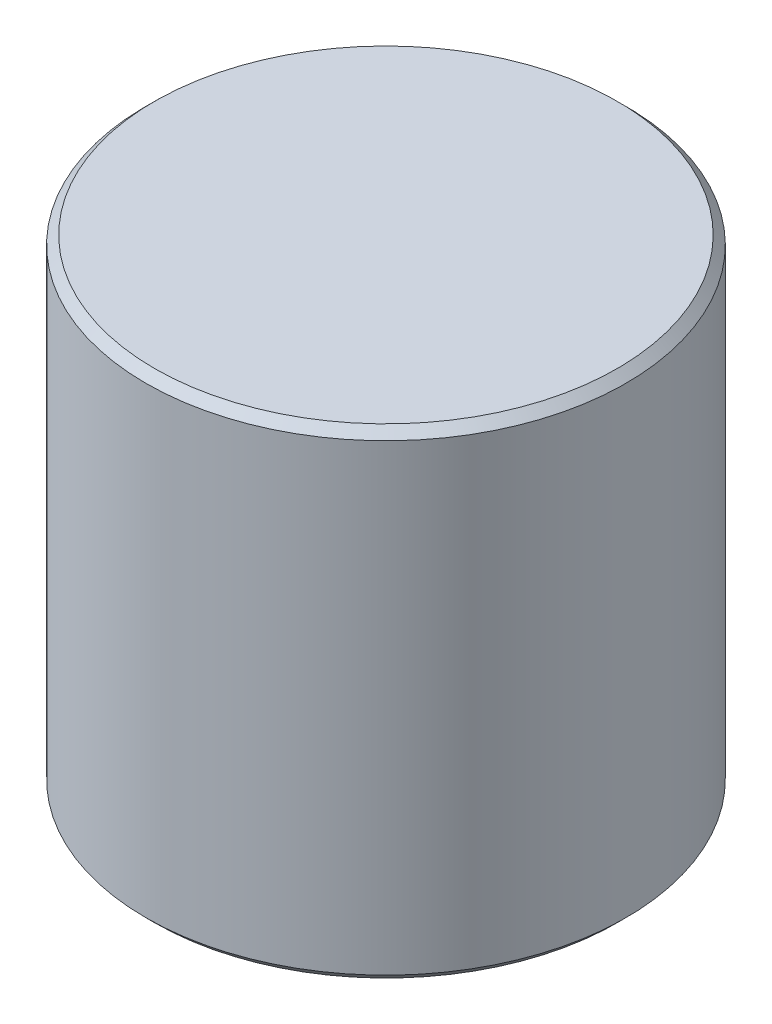
SolidWorks part; units mm, degrees
material "AISI 416 Annealed Stainless Steel (SS)"
ref_plane "Front Plane" through (0, 0, 0) normal (0, 0, 1) x (1, 0, 0)
ref_plane "Top Plane" through (0, 0, 0) normal (0, 1, 0) x (1, 0, 0)
ref_plane "Right Plane" through (0, 0, 0) normal (1, 0, 0) x (0, 0, -1)
ref_plane "Plane1" through (0, 0, 0) normal (0, -1, 0) x (1, 0, 0)
sketch "Sketch1" plane through (0, 0, 0) normal (0, -1, 0) x (1, 0, 0)
  circle A0 centre (0, 0) radius 17.78
  dimension "D1" = 35.56
extrude "Boss-Extrude1" add sketch "Sketch1" against normal blind 35.56
sketch "Sketch2" plane through (0, 0, 0) normal (0, -1, 0) x (1, 0, 0)
  circle A0 centre (0, 0) radius 10.5
  dimension "D1" = 21
extrude "Cut-Extrude1" cut sketch "Sketch2" against normal blind 1
chamfer "Chamfer1" distance 0.635 angle 45 1 edges at (0, 0, 17.78)
chamfer "Chamfer2" distance 0.635 angle 45 1 edges at (0, 35.56, 17.78)
